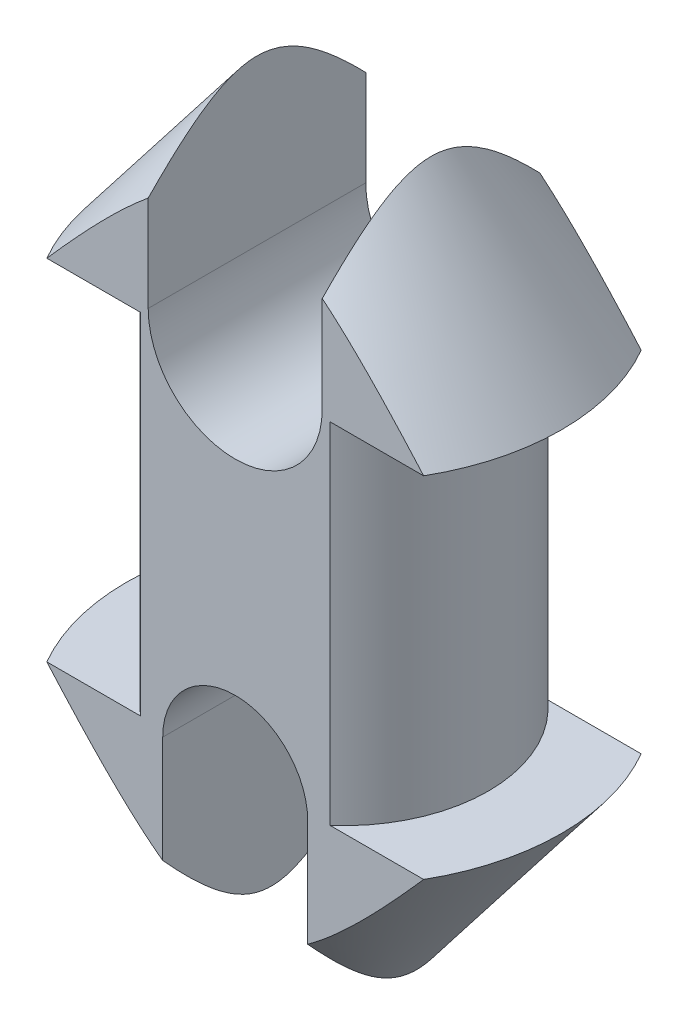
SolidWorks part; units mm, degrees
ref_plane "Plano frontal" through (0, 0, 0) normal (0, 0, 1) x (1, 0, 0)
ref_plane "Plano superior" through (0, 0, 0) normal (0, 1, 0) x (1, 0, 0)
ref_plane "Plano direito" through (0, 0, 0) normal (1, 0, 0) x (0, 0, -1)
sketch "Esboço1" plane through (0, 0, 0) normal (0, 0, 1) x (1, 0, 0)
  line L0 (0, -12.05) -> (0, 12.05) construction
  line L1 (-15, -12.05) -> (-15, 12.05)
  line L2 (15, -12.05) -> (15, 12.05)
  line L3 (15, 12.05) -> (9.95, 12.05)
  line L4 (9.95, 12.05) -> (9.95, -12.05)
  line L5 (9.95, -12.05) -> (15, -12.05)
  line L6 (0, 27.05) -> (0, -27.05)
  line L7 (0, -27.05) -> (0, 85.7647) construction
  line L8 (15, 12.05) -> (4, 26.5068)
  line L9 (15, -12.05) -> (4, -26.5068)
  arc A0 (-15, -12.05) -> (15, -12.05) centre (0, -12.05) ccw
  arc A1 (15, 12.05) -> (-15, 12.05) centre (0, 12.05) ccw
  point P2 (0, 0)
  dimension "D1" = 15
  dimension "D2" = 19.9
  dimension "D3" = 24.1
  dimension "D4" = 4
  dimension "D5" = 4
revolve "Revolução1" add sketch "Esboço1" angle 360 about L7
sketch "Esboço2" plane through (0, 0, 0) normal (0, 1, 0) x (1, 0, 0)
  line L1 (-15, -7.5) -> (15, -7.5)
  line L2 (-15, -7.5) -> (-15, 7.5)
  line L3 (-15, 7.5) -> (15, 7.5)
  line L4 (15, -7.5) -> (15, 7.5)
  line L5 (-15, -7.5) -> (15, 7.5) construction
  line L6 (-15, 7.5) -> (15, -7.5) construction
  circle A0 centre (0, 0) radius 15 construction
  point P0 (0, 0)
  dimension "D1" = 15
extrude "Corte-extrusão1" cut sketch "Esboço2" against normal through all both and the other way through all flip side to cut
sketch "Esboço3" plane through (0, 0, -7.5) normal (0, 0, -1) x (-1, 0, 0)
  line L0 (0, 27.05) -> (0, 12.55) construction
  line L1 (6, 27.05) -> (6, 12.55)
  line L2 (-6, 27.05) -> (-6, 12.55)
  line L3 (0, -27.05) -> (0, -12.55) construction
  line L4 (-5, -27.05) -> (-5, -12.55)
  line L5 (5, -27.05) -> (5, -12.55)
  arc A0 (4, 26.5068) -> (-4, 26.5068) centre (0, 12.05) ccw construction
  arc A1 (6, 27.05) -> (-6, 27.05) centre (0, 27.05) ccw
  arc A2 (-6, 12.55) -> (6, 12.55) centre (0, 12.55) ccw
  arc A3 (-4, -26.5068) -> (4, -26.5068) centre (0, -12.05) ccw construction
  arc A4 (-5, -27.05) -> (5, -27.05) centre (0, -27.05) ccw
  arc A5 (5, -12.55) -> (-5, -12.55) centre (0, -12.55) ccw
  point P6 (0, 19.8)
  point P11 (0, -19.8)
  dimension "D3" = 6
  dimension "D4" = 5
  dimension "D1" = 14.5
  dimension "D2" = 14.5
extrude "Corte-extrusão2" cut sketch "Esboço3" against normal through all
